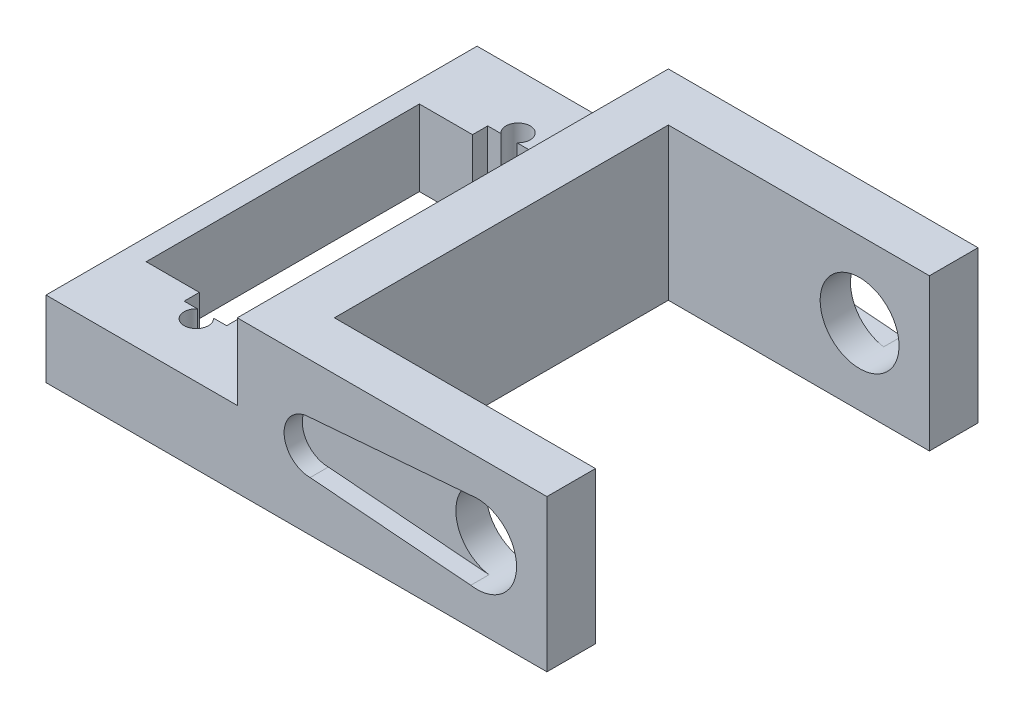
SolidWorks part; units mm, degrees
ref_plane "Front Plane" through (0, 0, 0) normal (0, 0, 1) x (1, 0, 0)
ref_plane "Top Plane" through (0, 0, 0) normal (0, 1, 0) x (1, 0, 0)
ref_plane "Right Plane" through (0, 0, 0) normal (1, 0, 0) x (0, 0, -1)
sketch "Sketch1" plane through (0, 0, 0) normal (0, 1, 0) x (1, 0, 0)
  line L1 (-20.955, 18.034) -> (20.955, 18.034)
  line L2 (-20.955, 18.034) -> (-20.955, -18.034)
  line L3 (-20.955, -18.034) -> (20.955, -18.034)
  line L4 (20.955, 18.034) -> (20.955, -18.034)
  line L5 (-20.955, 18.034) -> (20.955, -18.034) construction
  line L6 (-20.955, -18.034) -> (20.955, 18.034) construction
  point P0 (0, 0)
  dimension "D1" = 41.91
  dimension "D2" = 36.068
extrude "Boss-Extrude1" add sketch "Sketch1" along normal blind 12.7
sketch "Sketch3" plane through (0, 12.7, 0) normal (0, 1, 0) x (1, 0, 0)
  line L0 (20.955, -18.034) -> (20.955, 18.034) construction
  line L1 (20.955, 13.97) -> (-0.889, 13.97)
  line L2 (20.955, 13.97) -> (20.955, -13.97)
  line L3 (20.955, -13.97) -> (-0.889, -13.97)
  line L4 (-0.889, 13.97) -> (-0.889, -13.97)
  line L5 (20.955, 18.034) -> (-20.955, 18.034) construction
  line L6 (-20.955, -18.034) -> (20.955, -18.034) construction
  dimension "D1" = 21.844
  dimension "D2" = 4.064
  dimension "D3" = 4.064
extrude "Cut-Extrude1" cut sketch "Sketch3" against normal through all
sketch "Sketch4" plane through (0, 12.7, 0) normal (0, 1, 0) x (1, 0, 0)
  line L0 (20.955, 18.034) -> (-20.955, 18.034) construction
  line L1 (-20.955, -18.034) -> (-4.953, -18.034)
  line L2 (-20.955, -18.034) -> (-20.955, 18.034)
  line L3 (-20.955, 18.034) -> (-4.953, 18.034)
  line L4 (-4.953, -18.034) -> (-4.953, 18.034)
  line L5 (-0.889, 13.97) -> (-0.889, -13.97) construction
  dimension "D1" = 4.064
extrude "Cut-Extrude2" cut sketch "Sketch4" against normal blind 6.35
sketch "Sketch5" plane through (0, 6.35, 0) normal (0, 1, 0) x (1, 0, 0)
  line L0 (-12.954, 18.034) -> (-12.954, -18.034) construction
  line L1 (-6.731, 11.43) -> (-19.177, 11.43)
  line L2 (-6.731, 11.43) -> (-6.731, -11.43)
  line L3 (-6.731, -11.43) -> (-19.177, -11.43)
  line L4 (-19.177, 11.43) -> (-19.177, -11.43)
  line L5 (-6.731, 11.43) -> (-19.177, -11.43) construction
  line L6 (-6.731, -11.43) -> (-19.177, 11.43) construction
  line L7 (-4.953, 18.034) -> (-20.955, 18.034) construction
  line L8 (-20.955, -18.034) -> (-4.953, -18.034) construction
  point P0 (-12.954, 0)
  point P5 (-12.954, 0)
  dimension "D1" = 12.446
  dimension "D2" = 22.86
extrude "Cut-Extrude3" cut sketch "Sketch5" against normal through all
sketch "Sketch6" plane through (0, 6.35, 0) normal (0, 1, 0) x (1, 0, 0)
  line L0 (-12.954, 11.43) -> (-12.954, -11.43) construction
  line L1 (-6.731, 11.43) -> (-19.177, 11.43) construction
  line L2 (-19.177, -11.43) -> (-6.731, -11.43) construction
  line L3 (-12.954, -12.7) -> (-12.954, -21.6541) construction
  line L4 (-11.176, -10.16) -> (-14.732, -10.16)
  line L5 (-11.176, -10.16) -> (-11.176, -12.7)
  line L6 (-11.176, -12.7) -> (-14.732, -12.7)
  line L7 (-14.732, -10.16) -> (-14.732, -12.7)
  line L8 (-11.176, -10.16) -> (-14.732, -12.7) construction
  line L9 (-11.176, -12.7) -> (-14.732, -10.16) construction
  line L12 (-14.732, 10.16) -> (-14.732, 12.7)
  line L13 (-11.176, 12.7) -> (-14.732, 12.7)
  line L14 (-11.176, 10.16) -> (-11.176, 12.7)
  line L15 (-11.176, 10.16) -> (-14.732, 10.16)
  circle A0 centre (-12.954, -13.462) radius 1.016
  circle A1 centre (-12.954, 13.462) radius 1.016
  point P12 (-12.954, -13.462)
  dimension "D4" = 2.032
  dimension "D1" = 2.54
  dimension "D2" = 3.556
  dimension "D3" = 0.762
sketch "Sketch7" plane through (0, 6.35, 0) normal (0, 1, 0) x (1, 0, 0)
  line L0 (-6.731, 0) -> (-26.0997, 0) construction
  line L1 (-6.731, -11.43) -> (-6.731, 11.43) construction
extrude "Cut-Extrude11" cut sketch "Sketch6" against normal blind 6.35 contours A1 | L14 L13 L12 L15 | L7 L6 L5 L4 | A0
sketch "Sketch8" plane through (0, 0, -18.034) normal (0, 0, -1) x (-1, 0, 0)
  line L3 (-20.955, 12.7) -> (-20.955, 0) construction
  line L4 (-1.143, 8.5274) -> (-15.113, 9.652)
  line L5 (-1.143, 4.1726) -> (-15.113, 3.048)
  circle A0 centre (-15.113, 6.35) radius 3.302
  circle A1 centre (-1.143, 6.35) radius 2.1774
  dimension "D1" = 2.54
  dimension "D2" = 13.97
  dimension "D3" = 6.604
extrude "Cut-Extrude13" cut sketch "Sketch8" against normal blind 1.524 contours A1 | A1 L4 A0 L5 | L4 A0 L5
mirror "Mirror1" about plane through (0, 0, 0) normal (0, 0, 1) of "Cut-Extrude13"
sketch "Sketch9" plane through (0, 0, -18.034) normal (0, 0, -1) x (-1, 0, 0)
  circle A1 centre (-15.113, 6.35) radius 3.302
  dimension "D1" = 6.604
extrude "Cut-Extrude14" cut sketch "Sketch9" against normal through all
